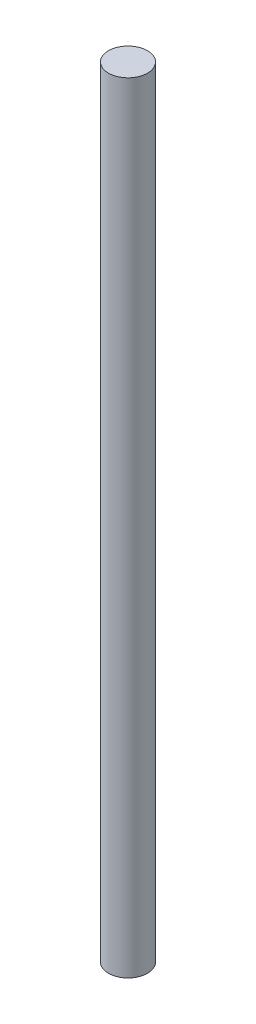
SolidWorks part; units mm, degrees
ref_plane "Front Plane" through (0, 0, 0) normal (0, 0, 1) x (1, 0, 0)
ref_plane "Top Plane" through (0, 0, 0) normal (0, 1, 0) x (1, 0, 0)
ref_plane "Right Plane" through (0, 0, 0) normal (1, 0, 0) x (0, 0, -1)
sketch "Sketch1" plane through (0, 0, 0) normal (0, 1, 0) x (1, 0, 0)
  circle A0 centre (0, 0) radius 3.81
  dimension "D1" = 7.62
extrude "Boss-Extrude1" add sketch "Sketch1" along normal mid plane 152.4
